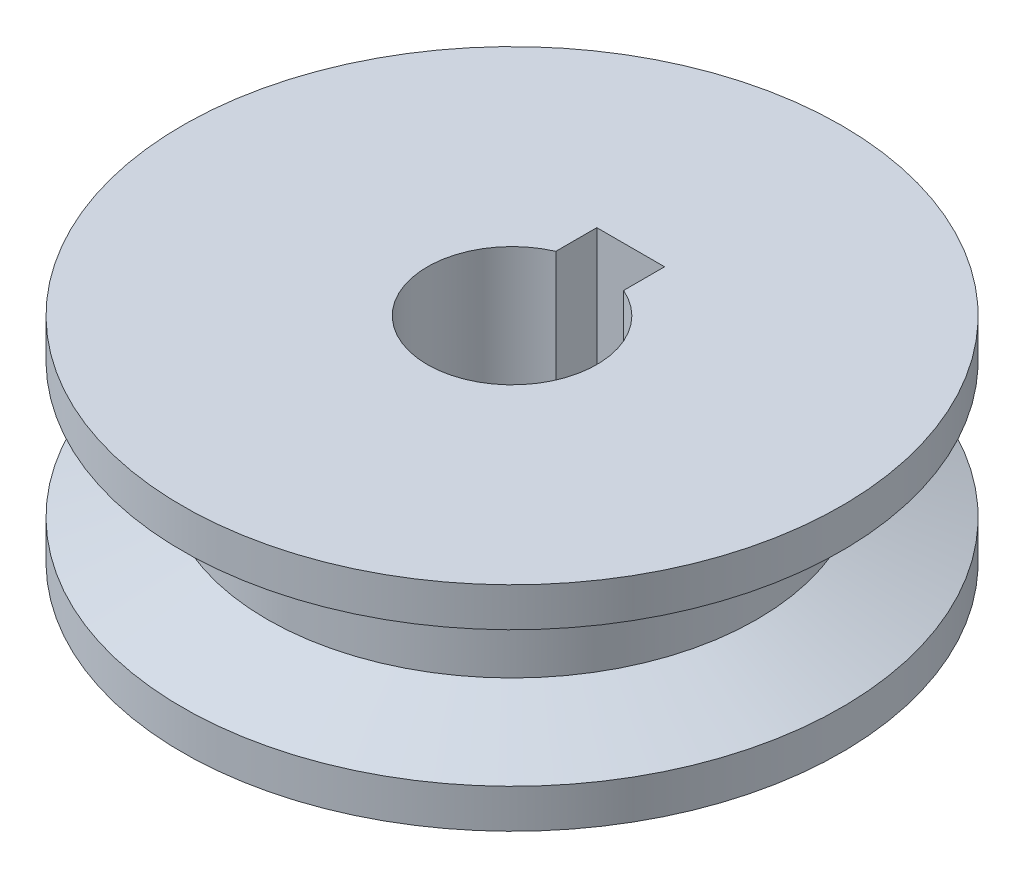
SolidWorks part; units mm, degrees
ref_plane "Alzado" through (0, 0, 0) normal (0, 0, 1) x (1, 0, 0)
ref_plane "Planta" through (0, 0, 0) normal (0, 1, 0) x (1, 0, 0)
ref_plane "Vista lateral" through (0, 0, 0) normal (1, 0, 0) x (0, 0, -1)
sketch "Croquis1" plane through (0, 0, 0) normal (0, 0, 1) x (1, 0, 0)
  line L0 (0, 0) -> (0, 59.2573) construction
  line L1 (7.9375, 0) -> (7.9375, 20)
  line L2 (7.9375, 20) -> (30.875, 20)
  line L3 (30.875, 20) -> (30.875, 16.35)
  line L4 (30.875, 16.35) -> (22.9375, 13.175)
  line L5 (22.9375, 13.175) -> (22.9375, 6.825)
  line L6 (22.9375, 6.825) -> (30.875, 3.65)
  line L7 (30.875, 3.65) -> (30.875, 0)
  line L8 (30.875, 0) -> (7.9375, 0)
  dimension "D1" = 12.7
  dimension "D2" = 6.35
  dimension "D3" = 7.9375
  dimension "D4" = 20
  dimension "D5" = 7.9375
  dimension "D6" = 15
revolve "Revolución2" add sketch "Croquis1" angle 360 about L0
sketch "Croquis2" plane through (0, 20, 0) normal (0, 1, 0) x (1, 0, 0)
  line L0 (0, 0) -> (0, 14.676) construction
  line L1 (-3.175, 4.7625) -> (3.175, 4.7625)
  line L2 (-3.175, 4.7625) -> (-3.175, 11.1125)
  line L3 (-3.175, 11.1125) -> (3.175, 11.1125)
  line L4 (3.175, 4.7625) -> (3.175, 11.1125)
  line L5 (-3.175, 7.9375) -> (3.175, 7.9375) construction
  circle A0 centre (0, 0) radius 7.9375
  circle A2 centre (0, 0) radius 7.9375 construction
  point P8 (0, 4.7625)
  circle M9 centre (0, 0) radius 7.9375
  dimension "D1" = 6.35
extrude "Cortar-Extruir1" cut sketch "Croquis2" against normal through all contours L4 L3 L2 M9
